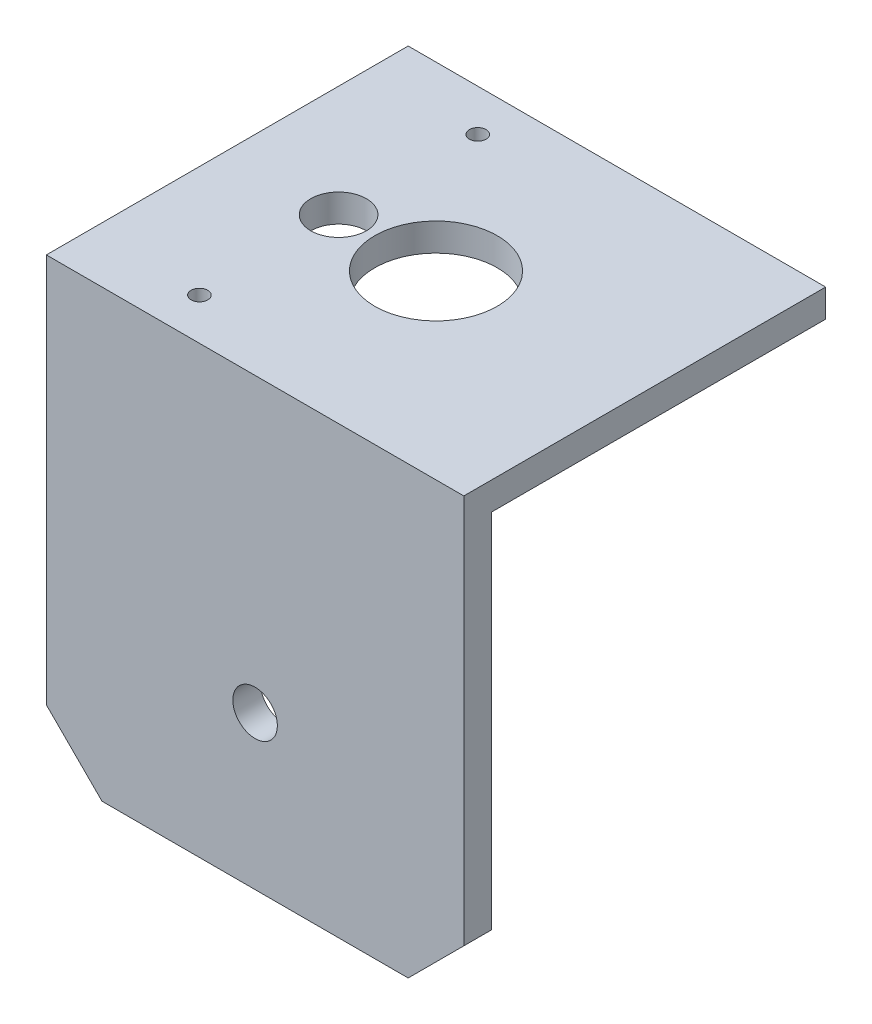
SolidWorks part; units mm, degrees
ref_plane "Ön Düzlem" through (0, 0, 0) normal (0, 0, 1) x (1, 0, 0)
ref_plane "Üst Düzlem" through (0, 0, 0) normal (0, 1, 0) x (1, 0, 0)
ref_plane "Sağ Düzlem" through (0, 0, 0) normal (1, 0, 0) x (0, 0, -1)
sketch "Sketch1" plane through (0, 0, 0) normal (0, 1, 0) x (1, 0, 0)
  line L1 (-37.5, 32.5) -> (37.5, 32.5)
  line L2 (-37.5, 32.5) -> (-37.5, -32.5)
  line L3 (-37.5, -32.5) -> (37.5, -32.5)
  line L4 (37.5, 32.5) -> (37.5, -32.5)
  line L5 (-37.5, 32.5) -> (37.5, -32.5) construction
  line L6 (-37.5, -32.5) -> (37.5, 32.5) construction
  circle A0 centre (-17.5, 0) radius 5
  circle A1 centre (0, 0) radius 11
  circle A2 centre (-17.5, -25) radius 1.5
  circle A3 centre (-17.5, 25) radius 1.5
  point P0 (0, 0)
  dimension "D3" = 10
  dimension "D4" = 22
  dimension "D8" = 3
  dimension "D9" = 3
  dimension "D1" = 75
  dimension "D2" = 65
  dimension "D5" = 17.5
  dimension "D6" = 50
  dimension "D7" = 25
extrude "Boss-Extrude1" add sketch "Sketch1" along normal blind 5
sketch "Sketch2" plane through (0, 0, 0) normal (0, -1, 0) x (1, 0, 0)
  line L0 (37.5, 32.5) -> (37.5, -32.5) construction
  line L1 (-37.5, 32.5) -> (37.5, 32.5)
  line L2 (-37.5, 32.5) -> (-37.5, 27.5)
  line L3 (-37.5, 27.5) -> (37.5, 27.5)
  line L4 (37.5, 32.5) -> (37.5, 27.5)
  line L6 (-37.5, -32.5) -> (37.5, -32.5)
  line L7 (-37.5, -32.5) -> (-37.5, -27.5)
  line L8 (-37.5, -27.5) -> (37.5, -27.5)
  line L9 (37.5, -32.5) -> (37.5, -27.5)
  dimension "D1" = 5
  dimension "D2" = 5
extrude "Boss-Extrude2" add sketch "Sketch2" along normal blind 75
sketch "Sketch3" plane through (0, 0, 32.5) normal (0, 0, 1) x (1, 0, 0)
  line L0 (-37.5, -75) -> (-27.5, -75)
  line L1 (37.5, -75) -> (-37.5, -75) construction
  line L2 (-27.5, -75) -> (-37.5, -65)
  line L3 (-37.5, 5) -> (-37.5, -75) construction
  line L4 (-37.5, -65) -> (-37.5, -75)
  line L5 (37.5, -75) -> (37.5, -65)
  line L6 (37.5, 5) -> (37.5, -75) construction
  line L7 (37.5, -65) -> (27.5, -75)
  line L8 (27.5, -75) -> (37.5, -75)
  dimension "D1" = 10
  dimension "D2" = 10
  dimension "D3" = 10
  dimension "D4" = 10
extrude "Cut-Extrude1" cut sketch "Sketch3" against normal up to next
sketch "Sketch4" plane through (0, 0, -27.5) normal (0, 0, 1) x (1, 0, 0)
  line L0 (-37.5, -75) -> (-27.5, -75)
  line L1 (-27.5, -75) -> (-37.5, -65)
  line L2 (-37.5, -65) -> (-37.5, -75)
  line L3 (27.5, -75) -> (37.5, -75)
  line L4 (37.5, -75) -> (37.5, -65)
  line L5 (37.5, -65) -> (27.5, -75)
  line L6 (27.5, -75) -> (17.494, -75.0141)
  line M2 (-37.5, 0) -> (-37.5, -75)
  line M3 (-37.5, -75) -> (37.5, -75)
  line M4 (37.5, -75) -> (37.5, 0)
extrude "Cut-Extrude2" cut sketch "Sketch4" against normal up to next contours L1 M3 M2 | L5 M4 M3
sketch "Sketch5" plane through (0, 0, 32.5) normal (0, 0, 1) x (1, 0, 0)
  line L0 (27.5, -75) -> (-27.5, -75) construction
  circle A0 centre (0, -47.5) radius 4
  dimension "D1" = 8
  dimension "D2" = 27.5
extrude "Cut-Extrude3" cut sketch "Sketch5" against normal up to next
sketch "Sketch6" plane through (0, 0, -32.5) normal (0, 0, -1) x (-1, 0, 0)
  circle A0 centre (0, -47.5) radius 2.5
extrude "Cut-Extrude4" cut sketch "Sketch6" against normal up to next
sketch "Sketch7" plane through (0, 0, -27.5) normal (0, 0, 1) x (1, 0, 0)
  line L0 (-37.5, 0) -> (37.5, 0)
  line L1 (37.5, 0) -> (37.5, -65)
  line L2 (37.5, -65) -> (27.5, -75)
  line L3 (27.5, -75) -> (-27.5, -75)
  line L4 (-27.5, -75) -> (-37.5, -65)
  line L5 (-37.5, -65) -> (-37.5, 0)
extrude "Cut-Extrude5" cut sketch "Sketch7" against normal up to next
